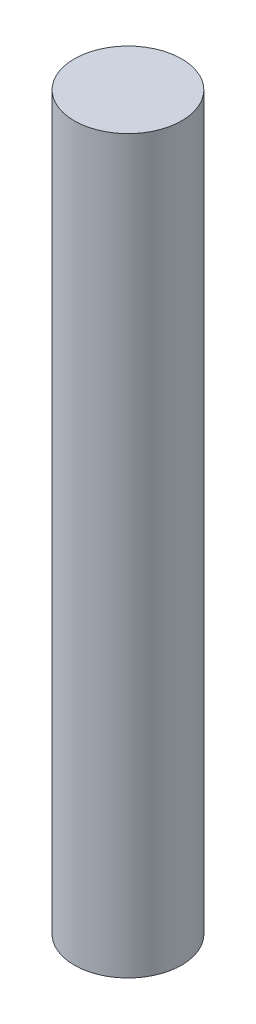
SolidWorks part; units mm, degrees
ref_plane "Front Plane" through (0, 0, 0) normal (0, 0, 1) x (1, 0, 0)
ref_plane "Top Plane" through (0, 0, 0) normal (0, 1, 0) x (1, 0, 0)
ref_plane "Right Plane" through (0, 0, 0) normal (1, 0, 0) x (0, 0, -1)
sketch "Sketch1" plane through (0, 0, 0) normal (0, 1, 0) x (1, 0, 0)
  circle A0 centre (0, 0) radius 1.27
  dimension "D1" = 2.54
extrude "Boss-Extrude1" add sketch "Sketch1" along normal blind 17.2974
